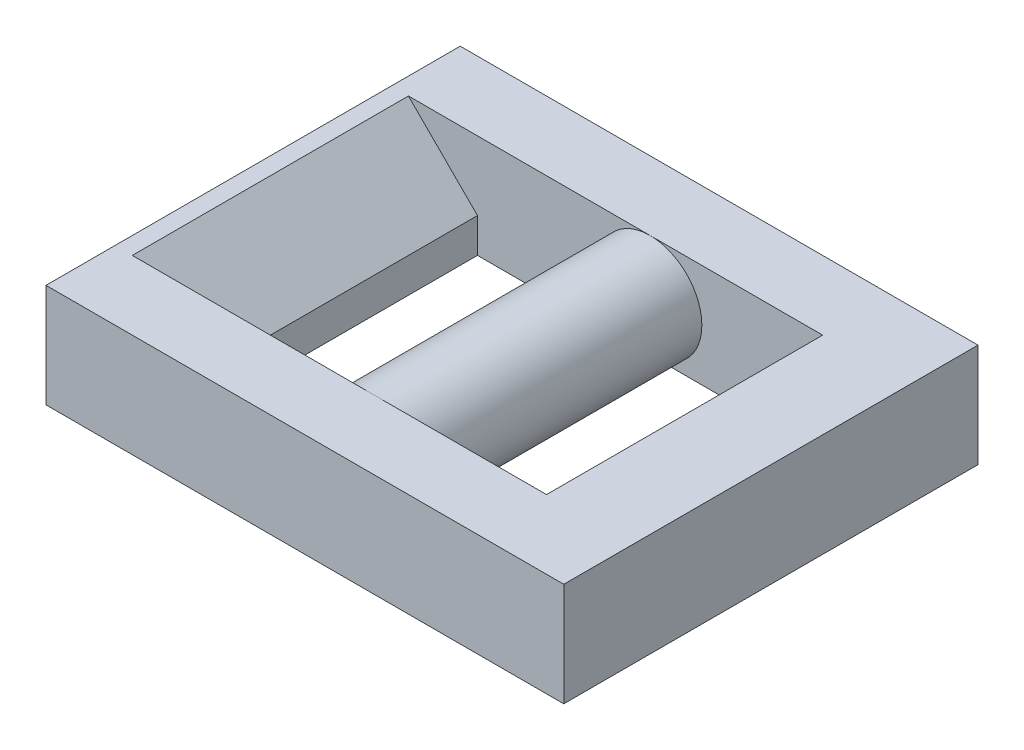
SolidWorks part; units mm, degrees
ref_plane "Front Plane" through (0, 0, 0) normal (0, 0, 1) x (1, 0, 0)
ref_plane "Top Plane" through (0, 0, 0) normal (0, 1, 0) x (1, 0, 0)
ref_plane "Right Plane" through (0, 0, 0) normal (1, 0, 0) x (0, 0, -1)
sketch "Sketch1" plane through (0, 0, 0) normal (0, 1, 0) x (1, 0, 0)
  line L1 (7.5, -6) -> (-7.5, -6)
  line L2 (7.5, -6) -> (7.5, 6)
  line L3 (7.5, 6) -> (-7.5, 6)
  line L4 (-7.5, -6) -> (-7.5, 6)
  line L5 (7.5, -6) -> (-7.5, 6) construction
  line L6 (7.5, 6) -> (-7.5, -6) construction
  line L7 (5, -4) -> (-5, -4)
  line L8 (5, -4) -> (5, 4)
  line L9 (5, 4) -> (-5, 4)
  line L10 (-5, -4) -> (-5, 4)
  line L11 (5, -4) -> (-5, 4) construction
  line L12 (5, 4) -> (-5, -4) construction
  point P0 (0, 0)
  point P6 (0, 0)
  dimension "D1" = 15
  dimension "D2" = 12
  dimension "D3" = 8
  dimension "D4" = 10
extrude "Boss-Extrude1" add sketch "Sketch1" along normal mid plane 3
sketch "Sketch2" plane through (0, 0, -4) normal (0, 0, 1) x (1, 0, 0)
  circle A0 centre (0, 0) radius 1.5
  dimension "D1" = 3
extrude "Boss-Extrude2" add sketch "Sketch2" along normal up to next
chamfer "Chamfer1" distance 2 angle 45 1 edges at (5, -1.5, 0)
chamfer "Chamfer2" distance 2 angle 45 1 edges at (-5, 1.5, 0)
